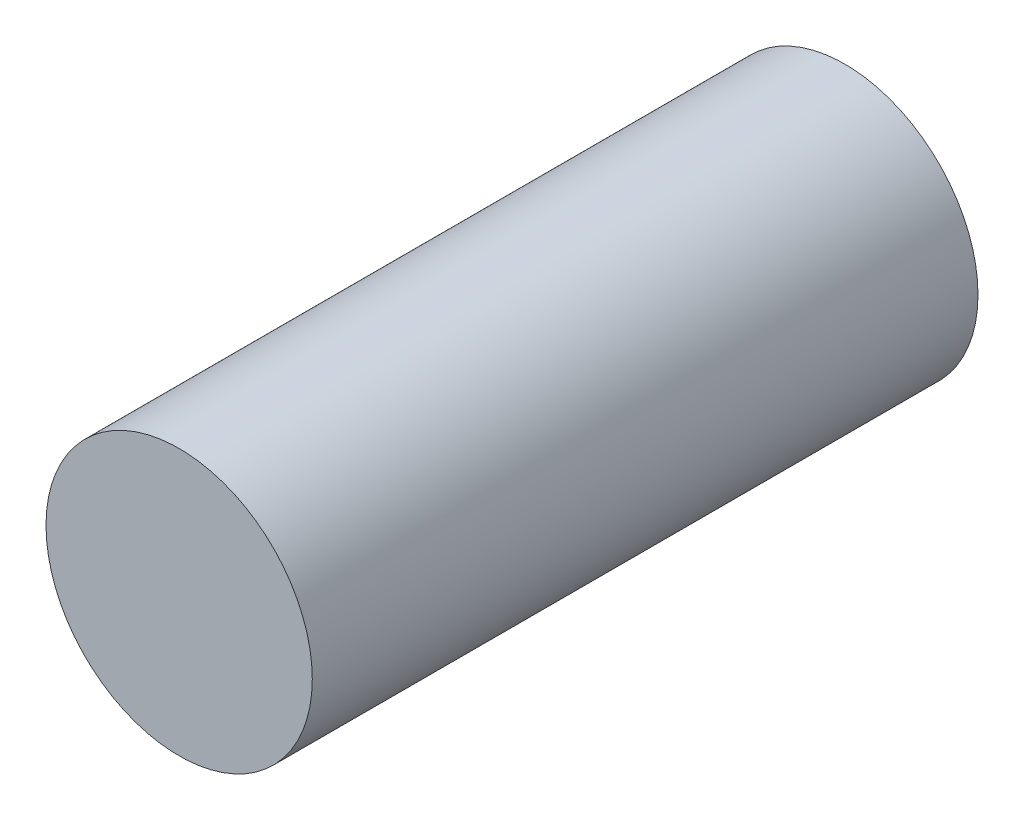
SolidWorks part; units mm, degrees
ref_plane "Front Plane" through (0, 0, 0) normal (0, 0, 1) x (1, 0, 0)
ref_plane "Top Plane" through (0, 0, 0) normal (0, 1, 0) x (1, 0, 0)
ref_plane "Right Plane" through (0, 0, 0) normal (1, 0, 0) x (0, 0, -1)
sketch "Sketch1" plane through (0, 0, 0) normal (0, 0, 1) x (1, 0, 0)
  circle A0 centre (-39.7871, 20.3483) radius 20
extrude "Boss-Extrude1" add sketch "Sketch1" along normal blind 100
